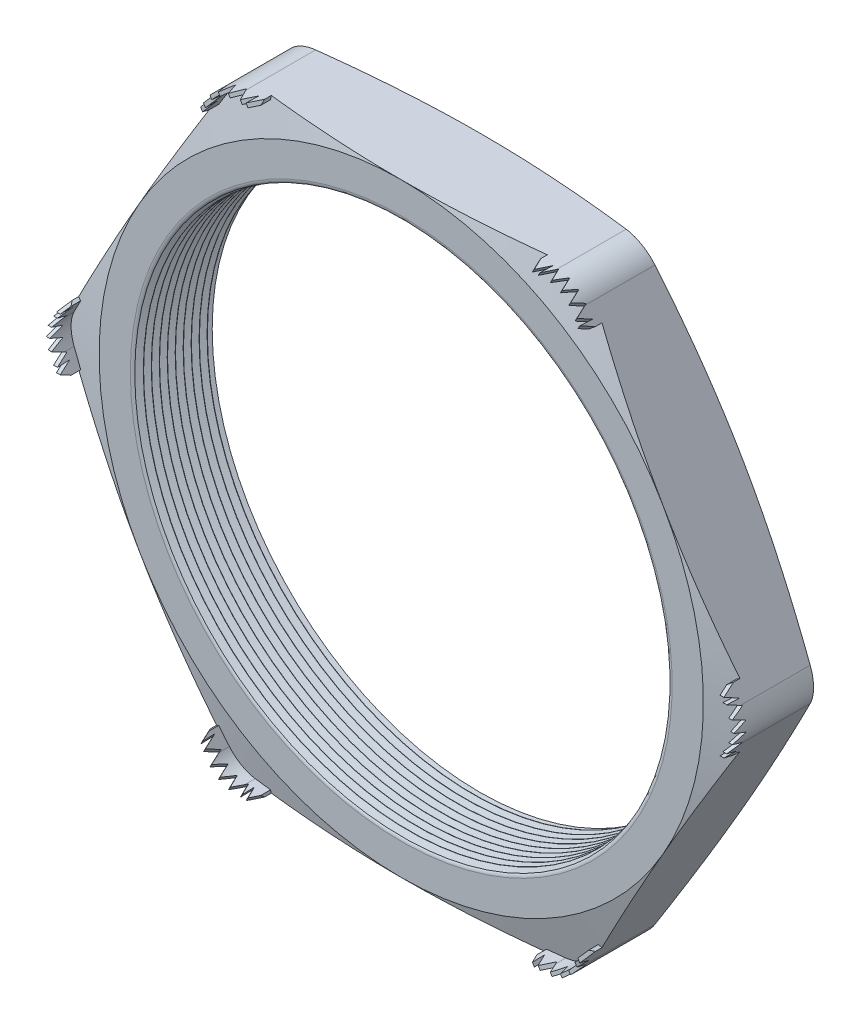
SolidWorks part; units mm, degrees
ref_plane "Front Plane" through (0, 0, 0) normal (0, 0, 1) x (1, 0, 0)
ref_plane "Top Plane" through (0, 0, 0) normal (0, 1, 0) x (1, 0, 0)
ref_plane "Right Plane" through (0, 0, 0) normal (1, 0, 0) x (0, 0, -1)
sketch "Sketch1" plane through (0, 0, 0) normal (0, 0, 1) x (1, 0, 0)
  line L1 (-13.3449, 0) -> (-6.6724, -11.557)
  line L2 (-6.6724, -11.557) -> (6.6724, -11.557)
  line L3 (6.6724, -11.557) -> (13.3449, 0)
  line L4 (13.3449, 0) -> (6.6724, 11.557)
  line L5 (6.6724, 11.557) -> (-6.6724, 11.557)
  line L6 (-6.6724, 11.557) -> (-13.3449, 0)
  circle A0 centre (0, 0) radius 11.557 construction
  circle A1 centre (0, 0) radius 10.16
  dimension "TS" = 20.32
  dimension "H" = 23.114
extrude "Extrude1" add sketch "Sketch1" along normal blind 3.048
fillet "Fillet1" radius 1.27 6 edges at (-6.6724, 11.557, 1.524) (-13.3449, 0, 1.524) (-6.6724, -11.557, 1.524) (6.6724, -11.557, 1.524) (13.3449, 0, 1.524) (6.6724, 11.557, 1.524)
sketch "Sketch2" plane through (0, 0, 3.048) normal (0, 0, 1) x (1, 0, 0)
  line L0 (-5.9392, 11.557) -> (-5.2788, 11.557)
  line L1 (5.9392, 11.557) -> (-5.9392, 11.557) construction
  line L2 (-7.0391, 10.922) -> (-7.3693, 10.3501)
  line L3 (-7.0391, 10.922) -> (-12.9783, 0.635) construction
  line L4 (-5.9392, 11.43) -> (-5.2788, 11.43)
  line L5 (-6.9291, 10.8585) -> (-7.2593, 10.2866)
  line L6 (-7.3693, 10.3501) -> (-7.2593, 10.2866)
  line L7 (-5.2788, 11.557) -> (-5.2788, 11.43)
  arc A0 (-5.9392, 11.43) -> (-6.9291, 10.8585) centre (-5.9392, 10.287) ccw
  arc A1 (-5.9392, 11.557) -> (-7.0391, 10.922) centre (-5.9392, 10.287) ccw construction
  arc A4 (-5.9392, 11.557) -> (-7.0391, 10.922) centre (-5.9392, 10.287) ccw
  dimension "D1" = 0.6604
  dimension "D2" = 0.6604
  dimension "OFFSET" = 0.127
fillet "Fillet3" radius 0.2032 2 edges at (10.16, 0, 0) (10.16, 0, 3.048)
sketch "Sketch3" plane through (0, 0, 0) normal (0, 1, 0) x (1, 0, 0)
  line L0 (-10.16, -3.048) -> (-10.16, -2.7547)
  line L2 (-10.16, -2.7547) -> (-10.414, -2.9014)
  line L3 (-10.414, -2.9014) -> (-10.16, -3.048)
  line L4 (-10.16, -0.2032) -> (-10.16, -2.8448) construction
  line L5 (-7.0391, -3.048) -> (-12.9783, -3.048) construction
  dimension "D1" = 60
  dimension "D2" = 60
  dimension "D3" = 0.254
revolve "Cut-Revolve1" cut sketch "Sketch3" angle 360 about axis through (0, 0, 3.048) along (0, 0, -1)
pattern_linear "LPattern1" count 10 spacing 0.3048 along (0, 0, -1) of "Cut-Revolve1"
sketch "Sketch4" plane through (0, 0, 0) normal (0, 0, -1) x (-1, 0, 0)
  line L0 (-12.9783, 0.635) -> (-7.0391, 10.922) construction
  circle A0 centre (0, 0) radius 11.557
extrude "Cut-Extrude1" cut sketch "Sketch4" against normal through all draft 75 flip side to cut
sketch "Sketch5" plane through (0, 0, 3.048) normal (0, 0, 1) x (1, 0, 0)
  line L0 (5.9392, 11.557) -> (-5.9392, 11.557) construction
  circle A0 centre (0, 0) radius 11.557
extrude "Cut-Extrude2" cut sketch "Sketch5" against normal through all draft 75 flip side to cut
extrude "Extrude2" add sketch "Sketch2" along normal blind 1.143 and the other way up to next
ref_plane "Plane1" through (-6.269, 10.8583, 0) normal (0.5, -0.866, 0) x (0.866, 0.5, 0)
sketch "Sketch7" plane through (-6.269, 10.8583, 0) normal (0.5, -0.866, 0) x (0.866, 0.5, 0)
  line L0 (-1.2069, 2.9909) -> (-1.0037, 3.4709)
  line L1 (-1.2069, 2.7403) -> (-1.2069, 4.191) construction
  line L2 (0, 1.3136) -> (0, 4.0135) construction
  line L4 (-1.0037, 3.4709) -> (-0.8005, 2.9909)
  line L5 (-0.4064, 3.4709) -> (-0.2032, 2.9909)
  line L6 (-0.8128, 3.4709) -> (-0.6096, 2.9909)
  line L7 (-0.2032, 2.9909) -> (0, 3.4709)
  line L8 (0, 3.4709) -> (0.2032, 2.9909)
  line L10 (0.4064, 3.4709) -> (0.6096, 2.9909)
  line L11 (0.8128, 3.4709) -> (1.016, 2.9909)
  line L12 (-0.8005, 2.9909) -> (-0.8128, 3.4709)
  line L13 (-0.6096, 2.9909) -> (-0.4064, 3.4709)
  line L14 (0.2032, 2.9909) -> (0.4064, 3.4709)
  line L15 (1.0037, 3.4709) -> (1.2069, 2.9909)
  line L16 (1.2069, 2.7403) -> (1.2069, 4.191) construction
  line L17 (-1.2069, 2.9909) -> (-1.2069, 4.191)
  line L19 (-1.2069, 4.191) -> (1.2069, 4.191)
  line L20 (1.2069, 4.191) -> (1.2069, 2.9909)
  line L23 (0.6096, 2.9909) -> (0.8128, 3.4709)
  line L25 (1.016, 2.9909) -> (1.0037, 3.4709)
  dimension "D1" = 1.2001
  dimension "D2" = 0.7201
  dimension "D3" = 0.2032
extrude "Cut-Extrude4" cut sketch "Sketch7" against normal through all
pattern_circular "CirPattern1" count 6 over 360 about axis through (0, 0, 0) along (0, 0, 1) of "Extrude2"
pattern_circular "CirPattern2" count 6 over 360 about axis through (0, 0, 0) along (0, 0, 1) of "Cut-Extrude4"
